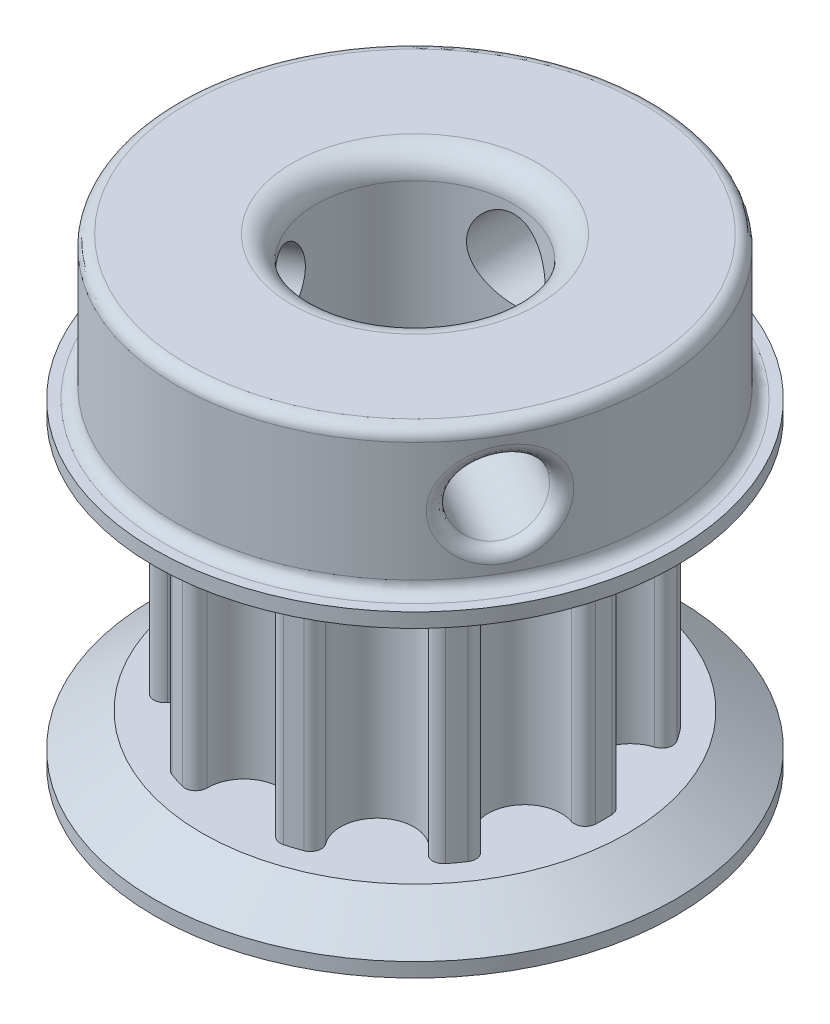
SolidWorks part; units mm, degrees
ref_plane "Plan de face" through (0, 0, 0) normal (0, 0, 1) x (1, 0, 0)
ref_plane "Plan de dessus" through (0, 0, 0) normal (0, 1, 0) x (1, 0, 0)
ref_plane "Plan de droite" through (0, 0, 0) normal (1, 0, 0) x (0, 0, -1)
sketch "Esquisse1" plane through (0, 0, 0) normal (0, 1, 0) x (1, 0, 0)
  line L0 (0, 0) -> (-2.449, 7.5372)
  line L2 (2.449, 7.5372) -> (0, 0)
  line L3 (0, 7.9251) -> (0, 0) construction
  line L4 (-2.449, 7.5372) -> (2.449, 7.5372) construction
  circle A1 centre (0, 0) radius 7.9251 construction
  arc A2 (-1.5429, 7.1881) -> (1.5429, 7.1881) centre (0, 7.1681) ccw
  arc A3 (-2.449, 7.5372) -> (-2.1236, 7.6353) centre (0, 0) cw
  arc A4 (-2.1236, 7.6353) -> (-1.5429, 7.1881) centre (-2.0008, 7.1941) cw
  arc A5 (2.449, 7.5372) -> (2.1236, 7.6353) centre (0, 0) ccw
  arc A6 (2.1236, 7.6353) -> (1.5429, 7.1881) centre (2.0008, 7.1941) ccw
  arc A7 (-1.5429, 7.1881) -> (-1.4081, 7.799) centre (0, 7.1681) cw construction
  arc A8 (1.5429, 7.1881) -> (1.4081, 7.799) centre (0, 7.1681) ccw construction
  point P0 (-1.2744, 9.7605)
  point P6 (0, 5.6251)
  point P20 (-0.8642, 8.7558)
  dimension "D2" = 1.543
  dimension "D3" = 0.458
  dimension "D1" = 4.898
  dimension "D4" = 2.3
  dimension "D5" = 36
extrude "Boss.-Extru.1" add sketch "Esquisse1" along normal blind 9.3
pattern_circular "Répétition circulaire1" count 10 over 360 about axis through (0, 0, 0) along (0, 1, 0) of "Boss.-Extru.1"
ref_plane "Plan1" through (0, 4.65, 0) normal (0, -1, 0) x (-1, 0, 0)
sketch "Esquisse2" plane through (0, 9.3, 0) normal (0, 1, 0) x (1, 0, 0)
  circle A0 centre (0, 0) radius 10.9251
  arc A1 (-6.2059, 4.9289) -> (-6.6054, 4.3791) centre (0, 0) ccw construction
  dimension "D1" = 3
extrude "Boss.-Extru.2" add sketch "Esquisse2" along normal blind 2
mirror "Symétrie1" about plane through (0, 4.65, 0) normal (0, -1, 0) of "Boss.-Extru.2"
chamfer "Chanfrein1" distance 2 angle 35 2 edges at (0, 9.3, 10.9251) (0, 0, 10.9251)
sketch "Esquisse4" plane through (0, 11.3, 0) normal (0, 1, 0) x (1, 0, 0)
  circle A0 centre (0, 0) radius 10
  dimension "D1" = 20
extrude "Boss.-Extru.3" add sketch "Esquisse4" along normal blind 6
sketch "Esquisse5" plane through (0, 0, 0) normal (0, 0, 1) x (1, 0, 0)
  line L0 (0, 0) -> (0, 14.3) construction
  line L1 (10, 17.3) -> (-10, 17.3) construction
  circle A0 centre (0, 14.3) radius 1.65
  point P3 (0, 14.6319)
  dimension "D2" = 3.3
  dimension "D1" = 3
extrude "Enlèv. mat.-Extru.2" cut sketch "Esquisse5" against normal through all
pattern_circular "Répétition circulaire2" count 3 over 360 about axis through (0, 17.3, 0) along (0, -1, 0) of "Enlèv. mat.-Extru.2"
sketch "Esquisse3" plane through (0, 17.3, 0) normal (0, 1, 0) x (1, 0, 0)
  circle A0 centre (0, 0) radius 4.15
  dimension "D1" = 8.3
extrude "Enlèv. mat.-Extru.1" cut sketch "Esquisse3" against normal up to next
fillet "Congé1" radius 1 2 edges at (0, -2, -4.15) (0, 17.3, 4.15)
fillet "Congé2" radius 0.5 5 edges at (0, 11.3, 10) (0, 17.3, 10) (0.3544, 12.6885, -9.9937) (-7.7413, 13.9455, 6.3302) (9.3528, 13.9455, 3.5391)
equation "\"nb_tooth\"= 10"
equation "\"D5@Esquisse1\"=360/\"nb_tooth\""
equation "\"D1@Répétition circulaire1\"=\"nb_tooth\""
